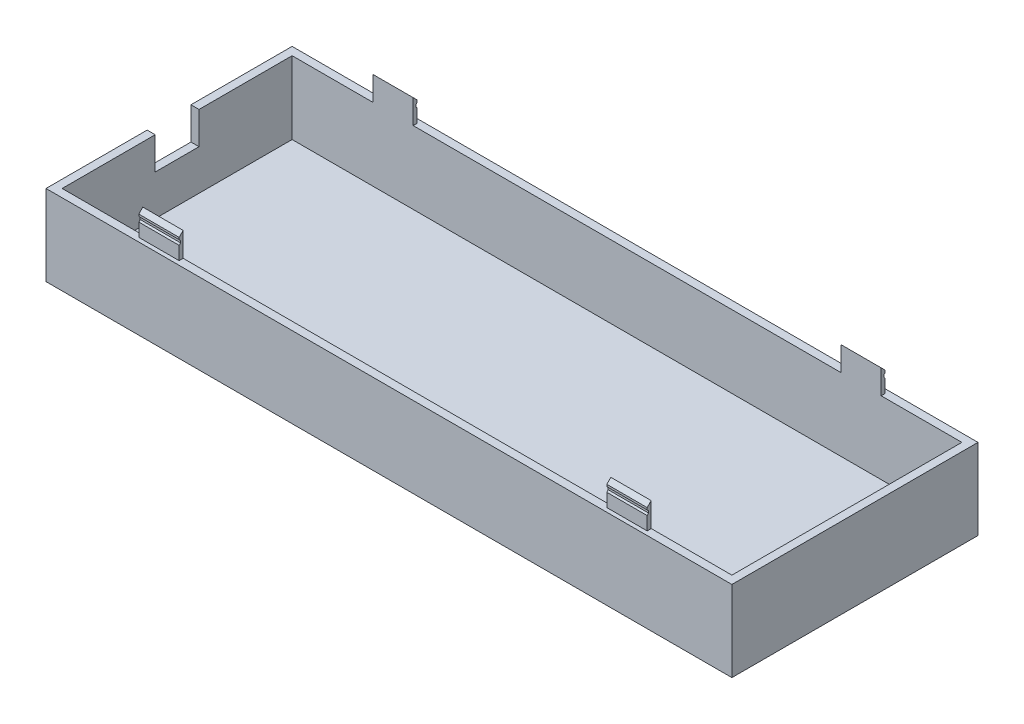
SolidWorks part; units mm, degrees
ref_plane "Front Plane" through (0, 0, 0) normal (0, 0, 1) x (1, 0, 0)
ref_plane "Top Plane" through (0, 0, 0) normal (0, 1, 0) x (1, 0, 0)
ref_plane "Right Plane" through (0, 0, 0) normal (1, 0, 0) x (0, 0, -1)
sketch "Sketch1" plane through (0, 0, 0) normal (0, 1, 0) x (1, 0, 0)
  line L1 (0, 0) -> (170, 0)
  line L2 (0, 0) -> (0, 61)
  line L3 (0, 61) -> (170, 61)
  line L4 (170, 0) -> (170, 61)
  dimension "D1" = 61
  dimension "D2" = 170
extrude "Boss-Extrude1" add sketch "Sketch1" along normal blind 20
sketch "Sketch2" plane through (0, 20, 0) normal (0, 1, 0) x (1, 0, 0)
  line L0 (0, 61) -> (0, 0) construction
  line L1 (2, 2) -> (168, 2)
  line L2 (2, 2) -> (2, 59)
  line L3 (2, 59) -> (168, 59)
  line L4 (168, 2) -> (168, 59)
  line L5 (170, 0) -> (170, 61) construction
  line L6 (0, 0) -> (170, 0) construction
  line L7 (170, 61) -> (0, 61) construction
  dimension "D1" = 2
  dimension "D2" = 2
  dimension "D3" = 2
  dimension "D4" = 2
extrude "Cut-Extrude1" cut sketch "Sketch2" against normal blind 18
sketch "Sketch3" plane through (0, 20, 0) normal (0, 1, 0) x (1, 0, 0)
  line L5 (2, 2) -> (168, 2) construction
  line L10 (22, 2) -> (32, 2)
  line L11 (22, 2) -> (22, 1)
  line L12 (22, 1) -> (32, 1)
  line L13 (32, 2) -> (32, 1)
  line L14 (168, 59) -> (2, 59) construction
  line L15 (138, 2) -> (148, 2)
  line L16 (138, 2) -> (138, 1)
  line L17 (138, 1) -> (148, 1)
  line L18 (148, 2) -> (148, 1)
  line L19 (22, 59) -> (32, 59)
  line L20 (22, 59) -> (22, 60)
  line L21 (22, 60) -> (32, 60)
  line L22 (32, 59) -> (32, 60)
  line L23 (0, 61) -> (0, 0) construction
  line L24 (138, 59) -> (148, 59)
  line L25 (138, 59) -> (138, 60)
  line L26 (138, 60) -> (148, 60)
  line L27 (148, 59) -> (148, 60)
  line L28 (170, 0) -> (170, 61) construction
  dimension "D1" = 1
  dimension "D2" = 1
  dimension "D3" = 1
  dimension "D4" = 1
  dimension "D5" = 10
  dimension "D6" = 10
  dimension "D7" = 10
  dimension "D8" = 10
  dimension "D9" = 22
  dimension "D10" = 22
  dimension "D11" = 22
  dimension "D12" = 22
extrude "Boss-Extrude2" add sketch "Sketch3" along normal blind 6
sketch "Sketch4" plane through (22, 0, 0) normal (-1, 0, 0) x (0, 0, 1)
  line L0 (-59, 26) -> (-60, 25)
  line L1 (-60, 26) -> (-60, 20) construction
  line L2 (-60, 25) -> (-60, 24.5)
  line L3 (-60, 24.5) -> (-59.6464, 24.1464)
  line L4 (-59.6464, 24.1464) -> (-59.6464, 23.6464)
  line L5 (-59.6464, 23.6464) -> (-60, 23.2929)
  line L6 (-60, 23.2929) -> (-60, 26)
  line L7 (-60, 26) -> (-59, 26)
  line L8 (-2, 26) -> (-1, 25)
  line L9 (-1, 26) -> (-1, 20) construction
  line L10 (-1, 25) -> (-1, 24.5)
  line L11 (-1, 24.5) -> (-1.3536, 24.1464)
  line L12 (-1.3536, 24.1464) -> (-1.3536, 23.6464)
  line L13 (-1.3536, 23.6464) -> (-1, 23.2929)
  line L14 (-1, 23.2929) -> (-1, 24.5)
  line L15 (-1, 26) -> (-2, 26)
  line L16 (-1, 25) -> (-1, 26)
  dimension "D1" = 0.5
  dimension "D2" = 0.5
  dimension "D3" = 0.5
  dimension "D4" = 0.5
  dimension "D5" = 0.5
  dimension "D6" = 0.5
  dimension "D7" = 45
  dimension "D8" = 45
extrude "Cut-Extrude2" cut sketch "Sketch4" against normal blind 200
sketch "Sketch5" plane through (0, 0, 0) normal (-1, 0, 0) x (0, 0, 1)
  line L0 (-30.5, 0) -> (-30.5, 12) construction
  line L1 (-61, 0) -> (0, 0) construction
  line L3 (-35.925, 12) -> (-25.075, 12)
  line L4 (-35.925, 12) -> (-35.925, 20)
  line L5 (-35.925, 20) -> (-25.075, 20)
  line L6 (-25.075, 12) -> (-25.075, 20)
  point P8 (0, 0)
  point P9 (0, 0)
  dimension "D1" = 12
  dimension "D2" = 5.425
  dimension "D3" = 10.85
  dimension "D4" = 8
extrude "Cut-Extrude3" cut sketch "Sketch5" against normal blind 5
